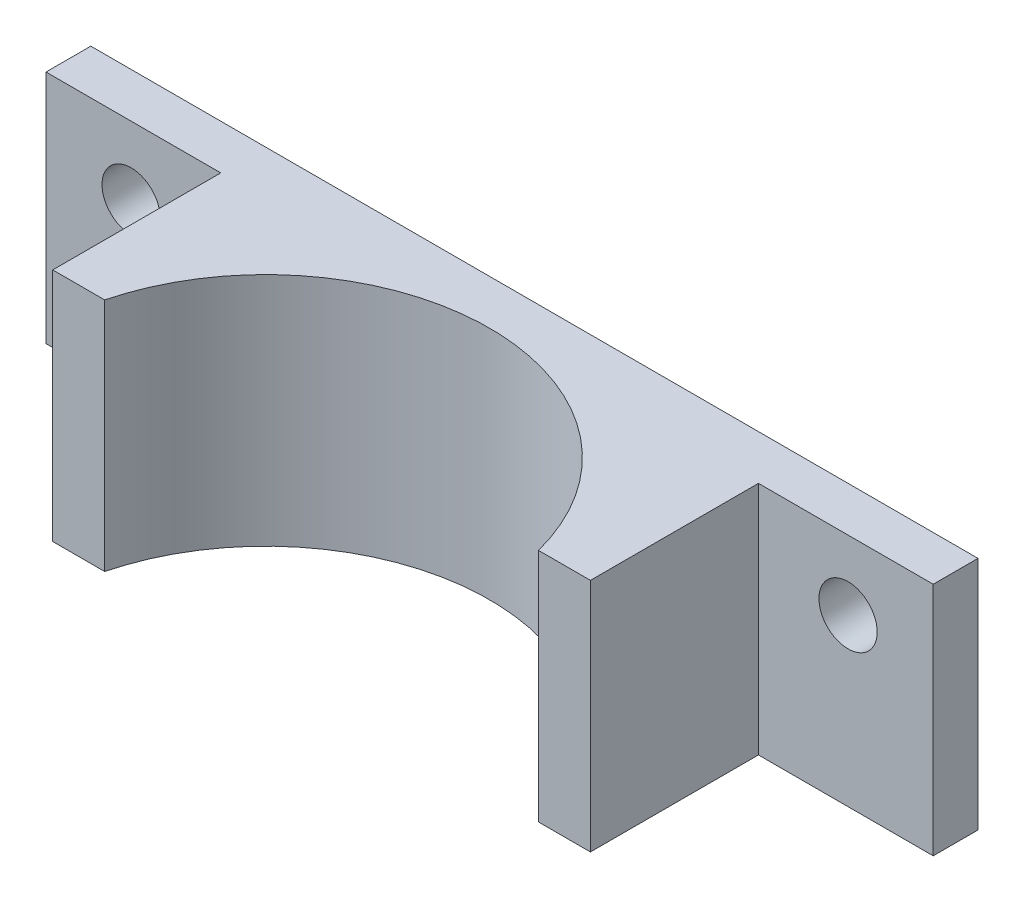
SolidWorks part; units mm, degrees
ref_plane "Front Plane" through (0, 0, 0) normal (0, 0, 1) x (1, 0, 0)
ref_plane "Top Plane" through (0, 0, 0) normal (0, 1, 0) x (1, 0, 0)
ref_plane "Right Plane" through (0, 0, 0) normal (1, 0, 0) x (0, 0, -1)
sketch "Sketch1" plane through (0, 0, 0) normal (0, 0, 1) x (1, 0, 0)
  line L1 (-60.27, 28.5994) -> (40.314, 28.5994)
  line L2 (-60.27, 28.5994) -> (-60.27, -24.7406)
  line L3 (-60.27, -24.7406) -> (40.314, -24.7406)
  line L4 (40.314, 28.5994) -> (40.314, -24.7406)
  circle A0 centre (30.662, 20.7254) radius 3.302
  circle A1 centre (30.662, -16.8666) radius 3.302
  circle A2 centre (-50.618, 20.7254) radius 3.302
  circle A3 centre (-50.618, -16.8666) radius 3.302
  dimension "D3" = 6.604
  dimension "D4" = 6.604
  dimension "D5" = 6.604
  dimension "D6" = 6.604
  dimension "D1" = 100.584
  dimension "D2" = 53.34
  dimension "D7" = 7.874
  dimension "D8" = 7.874
  dimension "D9" = 9.652
  dimension "D10" = 9.652
  dimension "D11" = 7.874
  dimension "D12" = 7.874
  dimension "D13" = 9.652
  dimension "D14" = 9.652
extrude "Boss-Extrude2" add sketch "Sketch1" along normal blind 5.08
sketch "Sketch5" plane through (0, 0, 5.08) normal (0, 0, 1) x (1, 0, 0)
  line L0 (40.314, 28.5994) -> (-60.27, 28.5994) construction
  line L1 (-40.458, 28.5994) -> (20.502, 28.5994)
  line L2 (-40.458, 28.5994) -> (-40.458, -24.7406)
  line L3 (-40.458, -24.7406) -> (20.502, -24.7406)
  line L4 (20.502, 28.5994) -> (20.502, -24.7406)
  line L5 (-60.27, -24.7406) -> (40.314, -24.7406) construction
  circle A0 centre (-50.618, -16.8666) radius 3.302 construction
  circle A1 centre (30.662, -16.8666) radius 3.302 construction
  dimension "D1" = 10.16
  dimension "D2" = 10.16
extrude "Boss-Extrude3" add sketch "Sketch5" along normal blind 19.05
sketch "Sketch6" plane through (0, -24.7406, 0) normal (0, -1, 0) x (1, 0, 0)
  line L0 (-60.27, 0) -> (40.314, 0) construction
  line L1 (-60.27, 5.08) -> (-60.27, 0) construction
  circle A0 centre (-9.978, 30.48) radius 25.4
  dimension "D1" = 50.8
  dimension "D2" = 30.48
  dimension "D3" = 50.292
extrude "Cut-Extrude4" cut sketch "Sketch6" against normal up to next
sketch "Sketch7" plane through (0, 0, 0) normal (0, 0, -1) x (-1, 0, 0)
  line L0 (-40.314, -24.7406) -> (-40.314, 28.5994) construction
  line L1 (-40.314, 1.9294) -> (60.27, 1.9294)
  line L2 (-40.314, 1.9294) -> (-40.314, -24.7406)
  line L3 (-40.314, -24.7406) -> (60.27, -24.7406)
  line L4 (60.27, 1.9294) -> (60.27, -24.7406)
  line L5 (60.27, 28.5994) -> (60.27, -24.7406) construction
  line L6 (60.27, -24.7406) -> (-40.314, -24.7406) construction
  dimension "D1" = 0
extrude "Cut-Extrude5" cut sketch "Sketch7" against normal through all
